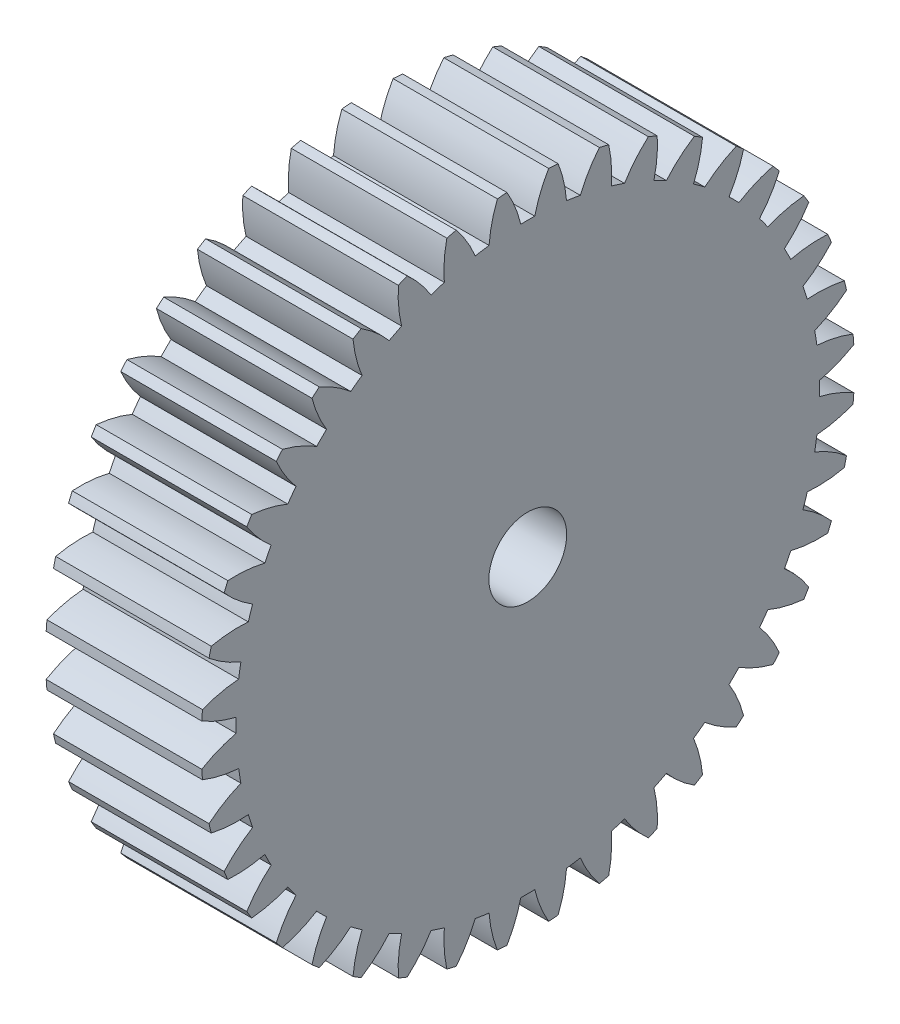
SolidWorks part; units mm, degrees
ref_plane "Plane1" through (0, 0, 0) normal (0, 0, 1) x (1, 0, 0)
ref_plane "Plane2" through (0, 0, 0) normal (0, 1, 0) x (1, 0, 0)
ref_plane "Plane3" through (0, 0, 0) normal (1, 0, 0) x (0, 0, -1)
other "Configuration Table"
sketch "HoldingSke" plane through (0, 0, 0) normal (0, 1, 0) x (1, 0, 0)
  line L0 (0, 0) -> (0.766, -0.6428)
  line L1 (-15, 0) -> (100, 0) construction
  line L2 (0, 0) -> (-2.1039, 2.3779)
  line L3 (0, 0) -> (-11.863, 4.5341)
  line L4 (0, 0) -> (6.6156, 5.5511)
  line L5 (0, 0) -> (-46.8476, -17.4728)
  line L6 (0, 0) -> (-8.2896, -5.593)
  line L7 (-2.1039, 2.3779) -> (8.6586, 51.2059)
  line L8 (-76.2, 54.61) -> (-75.3, 54.61)
  line L9 (-71.009, 38.7566) -> (-53.1078, 45.2721)
  line L10 (-76.2, 71.12) -> (104.1128, 71.12)
  line L11 (0, 0) -> (-10, 0)
  line L12 (-76.2, 101.6) -> (-76.162, 101.6)
  line L13 (24.9733, 27.94) -> (52.9518, 28.4284)
  line L14 (24.9733, 27.94) -> (24.9743, 27.94)
  line L15 (24.9733, 27.94) -> (100.4006, 29.5858)
  line L16 (-63.627, -1) -> (-12.827, -1)
  circle A0 centre (0, 0) radius 2.5
  circle A1 centre (0, 0) radius 18.749
  circle A2 centre (0, 0) radius 37.5
  circle A3 centre (0, 0) radius 2.5
  dimension "MHD" = 37.498
  dimension "Hub_dia" = 75
  dimension "Bore" = 5
  dimension "MBD" = 5
  dimension "Num_teeth" = 40
  dimension "Pitch" = 1
  dimension "Overall_len" = 50
  dimension "Show_teeth" = 40
  dimension "Thickness" = 10
  dimension "OAL" = 50.0001
  dimension "T_dim" = 0.9
  dimension "Ap" = 20
  dimension "H" = 19.05
  dimension "Pitch_radius" = 180.3128
  dimension "Width" = 10
  dimension "Backlash" = 0.038
  dimension "Addendum_fac" = 1
  dimension "Dedendum_fac" = 1.25
  dimension "Clearance_fac" = 0.25
  dimension "Dedendum_add" = 0.001
  dimension "Module" = 1
sketch "BasProSke" plane through (0, 0, 0) normal (0, 1, 0) x (1, 0, 0)
  line L0 (-10, 0) -> (60, 0) construction
  line L1 (0, 0) -> (0, 21)
  line L2 (0, 0) -> (10, 0)
  line L3 (10, 0) -> (10, 21)
  line L4 (10, 21) -> (0, 21)
  dimension "Thickness" = 10
  dimension "Diameter" = 42
revolve "Base-Revolve" add sketch "BasProSke" angle 360 about L0
sketch "TooCutSke" plane through (0, 0, 0) normal (1, 0, 0) x (0, 0, -1)
  line L1 (0, 0) -> (0, 107) construction
  line L2 (0, 0) -> (-0.8517, 19.9819) construction
  line L3 (0, 0) -> (-3.1363, 39.8509) construction
  line L4 (-0.8517, 19.9819) -> (-1.5682, 19.9255) construction
  arc A0 (0.4487, 18.7436) -> (-0.4487, 18.7436) centre (0, 0) ccw
  arc A1 (1.3547, 20.9817) -> (-1.3547, 20.9817) centre (0, 0) ccw
  circle A2 centre (0, 0) radius 20 construction
  circle A3 centre (0, 0) radius 18.7939 construction
  arc A4 (-0.4487, 18.7436) -> (-1.3547, 20.9817) centre (-8.2322, 16.895) ccw
  arc A5 (1.3547, 20.9817) -> (0.4487, 18.7436) centre (8.2322, 16.895) ccw
  dimension "Root_dia" = 37.498
  dimension "Overcut_dia" = 42.0508
  dimension "Pitch_dia" = 40
  dimension "Base_dia" = 37.5877
  dimension "Flank_rad" = 8
  dimension "Half_ang" = 4.5
  dimension "Half_CT" = 0.7187
extrude "ToothCut" cut sketch "TooCutSke" along normal through all
fillet "Breaks" [suppressed] radius 0.02
fillet "RootFillets" [suppressed] radius 0.251
pattern_circular "TeethCuts" count 40 every 9 about axis through (-10, 0, 0) along (1, 0, 0) of "ToothCut", "RootFillets", "Breaks"
sketch "HubNeaOneSke" plane through (0, 0, 0) normal (-1, 0, 0) x (0, 0, 1)
  circle A0 centre (0, 0) radius 18.749
  dimension "Diameter" = 37.498
extrude "HubNearOne" [suppressed] add sketch "HubNeaOneSke" along normal blind 40.0001
sketch "HubNeaBotSke" plane through (0, 0, 0) normal (-1, 0, 0) x (0, 0, 1)
  circle A0 centre (0, 0) radius 18.749
  dimension "Diameter" = 37.498
extrude "HubNearBoth" [suppressed] add sketch "HubNeaBotSke" along normal blind 20
ref_plane "FarPln" through (10, 0, 0) normal (1, 0, 0) x (0, 0, -1)
sketch "HubFarSke" plane through (10, 0, 0) normal (1, 0, 0) x (0, 0, -1)
  circle A0 centre (0, 0) radius 18.749
  dimension "Diameter" = 37.498
extrude "HubFar" [suppressed] add sketch "HubFarSke" along normal blind 20
sketch "BorSke" plane through (0, 0, 0) normal (1, 0, 0) x (0, 0, -1)
  circle A0 centre (0, 0) radius 2.5
  dimension "Diameter" = 5
extrude "Bore" cut sketch "BorSke" along normal mid plane 100.0001
sketch "KeySke" plane through (0, 0, 0) normal (1, 0, 0) x (0, 0, -1)
  line L0 (-1, 0) -> (-1, 3.4)
  line L1 (-1, 3.4) -> (1, 3.4)
  line L2 (1, 3.4) -> (1, 0)
  line L3 (0, 0) -> (0, 34) construction
  line L4 (-1, 0) -> (1, 0)
  dimension "Offset" = 3.4
  dimension "Width" = 2
extrude "Keyway" [suppressed] cut sketch "KeySke" along normal mid plane 100.0001
pattern_circular "Keyway2" [suppressed] count 2 every 90 about axis through (-10, 0, 0) along (1, 0, 0)
equation "' \"Module@HoldingSke\" = 6.35"
equation "' \"Num_teeth@HoldingSke\" = 12"
equation "' \"Ap@HoldingSke\" =  20"
equation "' \"Ap@HoldingSke\" = 20"
equation "' \"Width@HoldingSke\" = 0.5 * 25.4"
equation "' \"Hub_dia@HoldingSke\"= 1 * 25.4"
equation "' \"Hub_dia@HoldingSke\" = 1 * 25.4"
equation "' \"Overall_len@HoldingSke\" = 1.0 * 25.4"
equation "' \"Bore@HoldingSke\" = 0.75 * 25.4"
equation "' \"T_dim@HoldingSke\" = 0.1 * 25.4"
equation "' \"Width@KeySke\" = 0.25 * 25.4"
equation "' \"Show_teeth@HoldingSke\" = 13"
equation "' \"Backlash@HoldingSke\" = 0.009 * 25.4"
equation "' \"Addendum_fac@HoldingSke\" = 1.0"
equation "' \"Dedendum_fac@HoldingSke\" = 1.25"
equation "' \"Dedendum_add@HoldingSke\" = 0.00005 * 25.4"
equation "' \"Clearance_fac@HoldingSke\" = 0.25"
equation "\"Pitch@HoldingSke\" = 1 / \"Module@HoldingSke\""
equation "\"Overcut_dia@TooCutSke\" = (\"Num_teeth@HoldingSke\" + 2 * \"Addendum_fac@HoldingSke\") / \"Pitch@HoldingSke\" + 0.002 * 25.4"
equation "\"Pitch_dia@TooCutSke\" = \"Num_teeth@HoldingSke\" / \"Pitch@HoldingSke\""
equation "\"Base_dia@TooCutSke\" = \"Num_teeth@HoldingSke\" / \"Pitch@HoldingSke\" * cos((\"Ap@HoldingSke\"  * 3.14159265 / 180))"
equation "\"Root_dia@TooCutSke\" = (\"Num_teeth@HoldingSke\" + 2) / \"Pitch@HoldingSke\" - 2 * (\"Addendum_fac@HoldingSke\" + \"Dedendum_fac@HoldingSke\") / \"Pitch@HoldingSke\" - \"Dedendum_add@HoldingSke\" * 2"
equation "\"Half_ang@TooCutSke\" = 180 / \"Num_teeth@HoldingSke\""
equation "\"Half_CT@TooCutSke\" = \"Num_teeth@HoldingSke\" / \"Pitch@HoldingSke\" * sin((3.14159265 / 2 / \"Num_teeth@HoldingSke\")) / 2 - 7 * \"Backlash@HoldingSke\" / 4"
equation "\"Flank_rad@TooCutSke\" = \"Num_teeth@HoldingSke\" / \"Pitch@HoldingSke\" / 5"
equation "\"Radius@RootFillets\" = \"Clearance_fac@HoldingSke\" / \"Pitch@HoldingSke\" + \"Dedendum_add@HoldingSke\""
equation "\"Break_rad@Breaks\" = 0.02 / \"Pitch@HoldingSke\""
equation "\"Thickness@HoldingSke\" = \"Width@HoldingSke\""
equation "\"OAL@HoldingSke\" = \"Thickness@HoldingSke\""
equation "\"MHD@HoldingSke\" = (\"Num_teeth@HoldingSke\" + 2) / \"Pitch@HoldingSke\" - 2 * (\"Addendum_fac@HoldingSke\" + \"Dedendum_fac@HoldingSke\")  / \"Pitch@HoldingSke\" - \"Dedendum_add@HoldingSke\" * 2"
equation "\"MBD@HoldingSke\" = (\"Num_teeth@HoldingSke\" + 2) / \"Pitch@HoldingSke\" - 2 * (\"Addendum_fac@HoldingSke\" + \"Dedendum_fac@HoldingSke\")  / \"Pitch@HoldingSke\" - \"Dedendum_add@HoldingSke\" * 2 - 0.002 * 25.4"
equation "\"MHD@HoldingSke\" = ((sgn( \"MHD@HoldingSke\" - \"Hub_dia@HoldingSke\" )-1)*( \"MHD@HoldingSke\" - \"Hub_dia@HoldingSke\" ))/-2+ \"Hub_dia@HoldingSke\""
equation "\"MBD@HoldingSke\" = ((sgn( \"MBD@HoldingSke\" - \"Bore@HoldingSke\" )-1)*( \"MBD@HoldingSke\" - \"Bore@HoldingSke\" ))/-2+ \"Bore@HoldingSke\""
equation "\"OAL@HoldingSke\" = ((sgn( \"OAL@HoldingSke\" - \"Overall_len@HoldingSke\" )+1)*( \"OAL@HoldingSke\" - \"Overall_len@HoldingSke\" ))/2 + \"Overall_len@HoldingSke\" + 0.000002 * 25.4"
equation "\"Num_teeth@TeethCuts\" = int( \"Show_teeth@HoldingSke\" ) + 1"
equation "\"Num_teeth@TeethCuts\" = ((sgn( \"Num_teeth@TeethCuts\" - \"Num_teeth@HoldingSke\" )-1)*( \"Num_teeth@TeethCuts\" - \"Num_teeth@HoldingSke\" ))/-2+ \"Num_teeth@HoldingSke\""
equation "\"Num_teeth@TeethCuts\" = ((sgn( \"Num_teeth@TeethCuts\" - 2.0)+1)*( \"Num_teeth@TeethCuts\" - 2.0))/2 +2.0"
equation "\"Angle@TeethCuts\" = 360.0 / \"Num_teeth@HoldingSke\""
equation "\"Diameter@BasProSke\" = (\"Num_teeth@HoldingSke\" + 2 * \"Addendum_fac@HoldingSke\") / \"Pitch@HoldingSke\""
equation "\"Thickness@BasProSke\"  = \"Thickness@HoldingSke\""
equation "' \"Fillet_rad@BasProSke\" =  \"Thickness@HoldingSke\" * 0.05"
equation "' \"Fillet_rad@BasProSke\" = \"Thickness@HoldingSke\" * 0.05"
equation "\"MHD@HoldingSke\" = ((sgn( \"MHD@HoldingSke\" - \"Root_dia@TooCutSke\" )-1)*( \"MHD@HoldingSke\" - \"Root_dia@TooCutSke\" ))/-2+ \"Root_dia@TooCutSke\""
equation "\"Diameter@HubNeaOneSke\" = \"MHD@HoldingSke\""
equation "\"Length@HubNearOne\" = \"OAL@HoldingSke\" - \"Thickness@BasProSke\""
equation "\"Diameter@HubNeaBotSke\" = \"MHD@HoldingSke\""
equation "\"Length@HubNearBoth\" = ( \"OAL@HoldingSke\" - \"Thickness@BasProSke\" ) / 2.0"
equation "\"Thickness@FarPln\" = \"Thickness@BasProSke\""
equation "\"Diameter@HubFarSke\" = \"MHD@HoldingSke\""
equation "\"Length@HubFar\" = ( \"OAL@HoldingSke\" - \"Thickness@BasProSke\" ) / 2.0"
equation "\"Diameter@BorSke\" = \"MBD@HoldingSke\""
equation "\"D1@Bore\" = \"OAL@HoldingSke\" * 2.0"
equation "\"D1@Keyway\" = \"OAL@HoldingSke\" * 2.0"
equation "\"Offset@KeySke\" = \"T_dim@HoldingSke\" + \"MBD@HoldingSke\" / 2.0"
